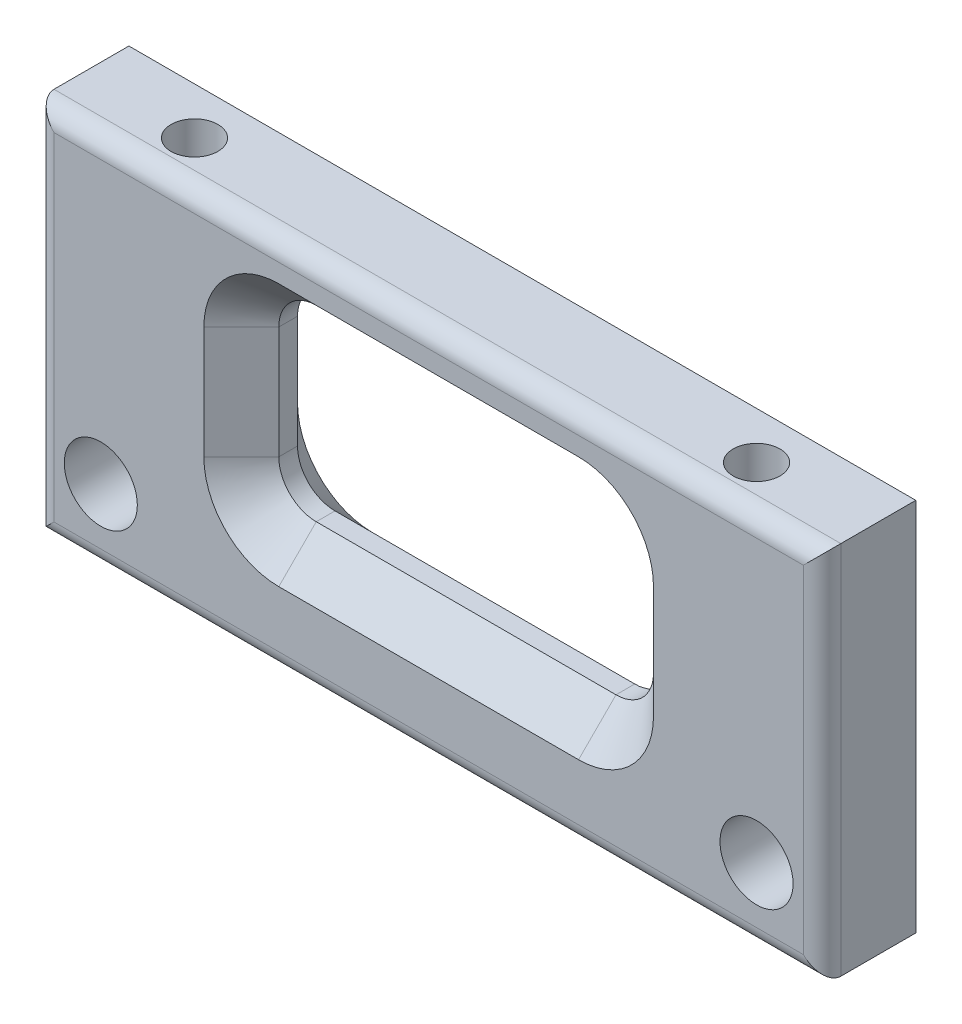
SolidWorks part; units mm, degrees
ref_plane "Ebene vorne" through (0, 0, 0) normal (0, 0, 1) x (1, 0, 0)
ref_plane "Ebene oben" through (0, 0, 0) normal (0, 1, 0) x (1, 0, 0)
ref_plane "Ebene rechts" through (0, 0, 0) normal (1, 0, 0) x (0, 0, -1)
sketch "Sketch1" plane through (0, 0, 0) normal (0, 0, 1) x (1, 0, 0)
  line L0 (0, -16) -> (42, -16) construction
  line L1 (0, 0) -> (42, 0)
  line L2 (0, 0) -> (0, -20)
  line L3 (0, -20) -> (42, -20)
  line L4 (42, 0) -> (42, -20)
  circle A1 centre (38.5, -16) radius 1.95
  circle A2 centre (3.5, -16) radius 1.95
  dimension "D5" = 3.9
  dimension "D1" = 20
  dimension "D2" = 4
  dimension "D3" = 35
  dimension "D4" = 42
  dimension "D6" = 3.5
extrude "Boss-Extrude1" add sketch "Sketch1" along normal blind 5
sketch "Sketch2" plane through (0, 0, 0) normal (0, 1, 0) x (1, 0, 0)
  line L0 (0, -2.5) -> (42, -2.5) construction
  line L1 (0, -5) -> (0, 0) construction
  line L2 (42, -5) -> (42, 0) construction
  circle A0 centre (36, -2.5) radius 1.25
  circle A1 centre (6, -2.5) radius 1.25
  dimension "D1" = 2.5
  dimension "D2" = 2.5
  dimension "D3" = 30
  dimension "D4" = 6
extrude "Cut-Extrude1" cut sketch "Sketch2" against normal blind 10
sketch "Sketch3" plane through (0, 0, 5) normal (0, 0, 1) x (1, 0, 0)
  line L0 (21, 0) -> (21, -20) construction
  line L1 (42, 0) -> (0, 0) construction
  line L2 (0, -20) -> (42, -20) construction
  line L4 (29, -13.9903) -> (13, -13.9903)
  line L5 (31, -11.9903) -> (31, -5.9903)
  line L6 (29, -3.9903) -> (13, -3.9903)
  line L7 (11, -11.9903) -> (11, -5.9903)
  line L8 (31, -13.9903) -> (11, -3.9903) construction
  line L9 (31, -3.9903) -> (11, -13.9903) construction
  arc A0 (13, -13.9903) -> (11, -11.9903) centre (13, -11.9903) cw
  arc A1 (29, -13.9903) -> (31, -11.9903) centre (29, -11.9903) ccw
  arc A2 (31, -5.9903) -> (29, -3.9903) centre (29, -5.9903) ccw
  arc A3 (11, -5.9903) -> (13, -3.9903) centre (13, -5.9903) cw
  point P6 (21, -8.9903)
  dimension "D3" = 2
  dimension "D1" = 20
  dimension "D2" = 10
extrude "Cut-Extrude2" cut sketch "Sketch3" against normal blind 10
fillet "Fillet1" radius 1 4 edges at (42, -10, 5) (21, 0, 5) (0, -10, 5) (21, -20, 5)
chamfer "Chamfer1" distance 2 angle 45 16 edges at (21, -3.9903, 0) (11.5858, -4.5761, 0) (30.4142, -4.5761, 0) (11, -8.9903, 0) (31, -8.9903, 0) (11.5858, -13.4046, 0) (30.4142, -13.4046, 0) (21, -13.9903, 0) (21, -3.9903, 5) (11.5858, -4.5761, 5) (30.4142, -4.5761, 5) (11, -8.9903, 5) (31, -8.9903, 5) (11.5858, -13.4046, 5) (30.4142, -13.4046, 5) (21, -13.9903, 5)
